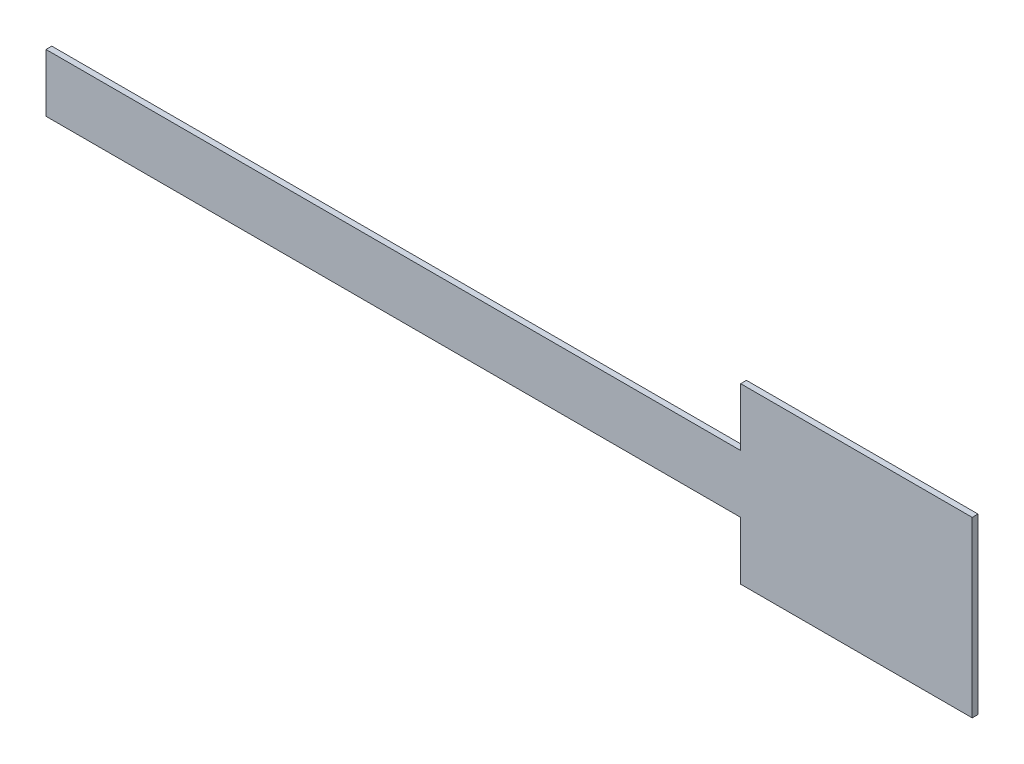
SolidWorks part; units mm, degrees
ref_plane "Front Plane" through (0, 0, 0) normal (0, 0, 1) x (1, 0, 0)
ref_plane "Top Plane" through (0, 0, 0) normal (0, 1, 0) x (1, 0, 0)
ref_plane "Right Plane" through (0, 0, 0) normal (1, 0, 0) x (0, 0, -1)
sketch "Sketch1" plane through (0, 0, 0) normal (0, 0, 1) x (1, 0, 0)
  line L0 (66.8161, 0.6865) -> (66.8161, -24.7135)
  line L1 (-237.9839, 26.0865) -> (66.8161, 26.0865)
  line L2 (-237.9839, 26.0865) -> (-237.9839, 0.6865)
  line L3 (-237.9839, 0.6865) -> (66.8161, 0.6865)
  line L4 (66.8161, 51.4865) -> (168.4161, 51.4865)
  line L5 (-237.9839, 26.0865) -> (66.8161, 0.6865) construction
  line L6 (-237.9839, 0.6865) -> (66.8161, 26.0865) construction
  line L7 (66.8161, 51.4865) -> (66.8161, 26.0865)
  line L8 (66.8161, -24.7135) -> (168.4161, -24.7135)
  line L9 (168.4161, 51.4865) -> (168.4161, -24.7135)
  point P0 (-85.5839, 13.3865)
  dimension "D1" = 304.8
  dimension "D2" = 25.4
  dimension "D3" = 101.6
  dimension "D4" = 76.2
extrude "Boss-Extrude2" add sketch "Sketch1" along normal blind 2.54
